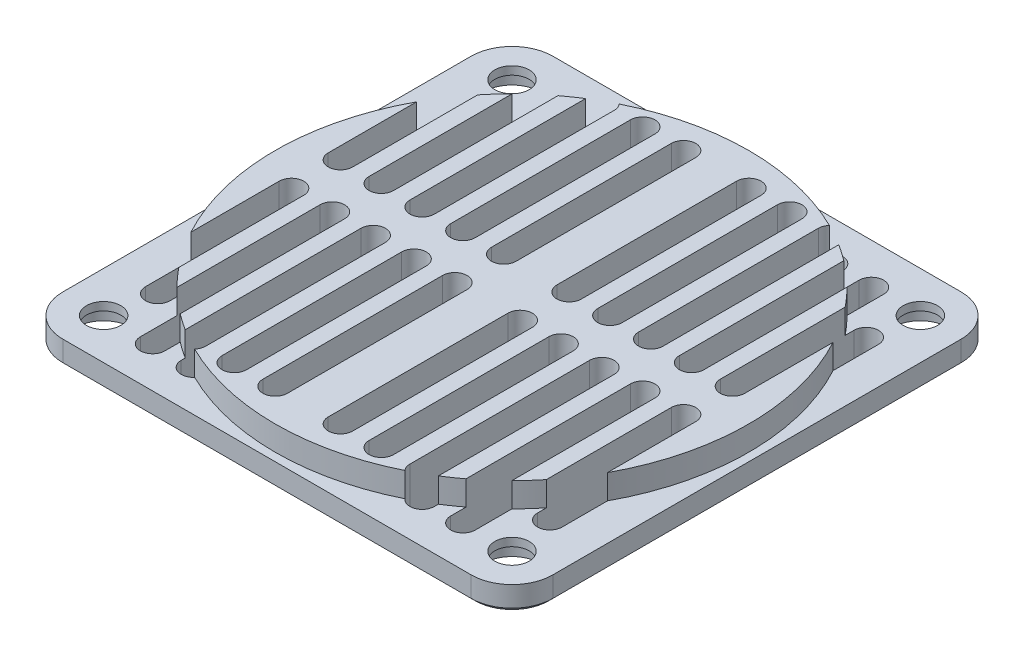
SolidWorks part; units mm, degrees
ref_plane "Alzado" through (0, 0, 0) normal (0, 0, 1) x (1, 0, 0)
ref_plane "Planta" through (0, 0, 0) normal (0, 1, 0) x (1, 0, 0)
ref_plane "Vista lateral" through (0, 0, 0) normal (1, 0, 0) x (0, 0, -1)
sketch "Croquis1" plane through (0, 0, 0) normal (0, 1, 0) x (1, 0, 0)
  line L0 (0, 0) -> (50000, 0) construction
  line L5 (0, 0) -> (30, 0)
  line L6 (0, 0) -> (0, 30)
  line L7 (0, 30) -> (30, 30)
  line L8 (30, 0) -> (30, 30)
  line L9 (0, 0) -> (30, 30) construction
  line L10 (0, 30) -> (30, 0) construction
  line L11 (0, 0) -> (0, 50000) construction
  line L12 (4, 3) -> (4, 25) construction
  line L13 (2.5, 3) -> (2.5, 25)
  line L14 (5.5, 3) -> (5.5, 25)
  line L15 (9, 3) -> (9, 25) construction
  line L16 (7.5, 3) -> (7.5, 25)
  line L17 (10.5, 3) -> (10.5, 25)
  line L18 (19, 3) -> (19, 25) construction
  line L19 (17.5, 3) -> (17.5, 25)
  line L20 (20.5, 3) -> (20.5, 25)
  line L21 (24, 3) -> (24, 19.3698) construction
  line L22 (22.5, 3) -> (22.5, 19.3698)
  line L23 (25.5, 3) -> (25.5, 19.3698)
  line L25 (14, 25) -> (14, 3) construction
  line L26 (15.5, 25) -> (15.5, 3)
  line L27 (12.5, 25) -> (12.5, 3)
  circle A3 centre (25, 25) radius 2.1
  arc A4 (2.5, 3) -> (5.5, 3) centre (4, 3) ccw
  arc A5 (5.5, 25) -> (2.5, 25) centre (4, 25) ccw
  arc A6 (7.5, 3) -> (10.5, 3) centre (9, 3) ccw
  arc A7 (10.5, 25) -> (7.5, 25) centre (9, 25) ccw
  arc A8 (17.5, 3) -> (20.5, 3) centre (19, 3) ccw
  arc A9 (20.5, 25) -> (17.5, 25) centre (19, 25) ccw
  arc A10 (22.5, 3) -> (25.5, 3) centre (24, 3) ccw
  arc A11 (25.5, 19.3698) -> (22.5, 19.3698) centre (24, 19.3698) ccw
  arc A12 (15.5, 25) -> (12.5, 25) centre (14, 25) ccw
  arc A13 (12.5, 3) -> (15.5, 3) centre (14, 3) ccw
  point P4 (15, 15)
  point P15 (4, 14)
  point P20 (9, 14)
  point P27 (19, 14)
  point P34 (24, 11.1849)
  point P41 (14, 14)
  point P43 (25, 11.1849)
  point P44 (0, 0)
  point P49 (4, 3)
  dimension "D2" = 50
  dimension "D1" = 4.2
  dimension "D5" = 1.5
  dimension "D3" = 60
  dimension "D4" = 50
  dimension "D6" = 5
  dimension "D7" = 8
  dimension "D8" = 5
  dimension "D9" = 5
  dimension "D10" = 5
extrude "Saliente-Extruir1" add sketch "Croquis1" along normal blind 6
fillet "Redondeo1" radius 5 1 edges at (30, 3, -30)
sketch "Croquis3" plane through (0, 0, 0) normal (0, -1, 0) x (1, 0, 0)
  circle A0 centre (25, -25) radius 3.45
  dimension "D1" = 6.9
extrude "Cortar-Extruir2" cut sketch "Croquis3" against normal blind 2
mirror "Simetría1" about plane through (0, 6, 0) normal (0, 0, -1) of "Cortar-Extruir2", "Saliente-Extruir1", "Redondeo1"
mirror "Simetría7" about plane through (0, 6, 0) normal (1, 0, 0) of bodies 102
sketch "Croquis2" plane through (0, 6, 0) normal (0, 1, 0) x (1, 0, 0)
  circle A0 centre (0, 0) radius 29
  dimension "D1" = 58
extrude "Cortar-Extruir1" cut sketch "Croquis2" against normal blind 3 flip side to cut
chamfer "Chaflán1" distance 0.5 angle 45 8 edges at (0, 0, 30) (28.5355, 0, 28.5355) (-28.5355, 0, 28.5355) (30, 0, 0) (-30, 0, 0) (28.5355, 0, -28.5355) (-28.5355, 0, -28.5355) (0, 0, -30)
